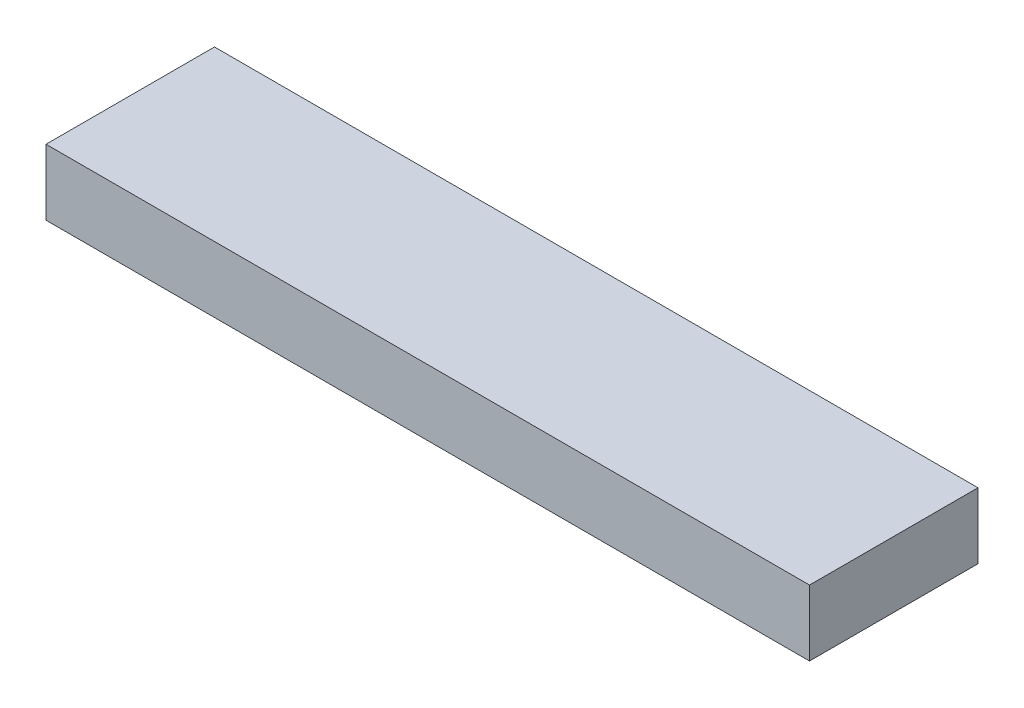
SolidWorks part; units mm, degrees
ref_plane "Front" through (0, 0, 0) normal (0, 0, 1) x (1, 0, 0)
ref_plane "Top" through (0, 0, 0) normal (0, 1, 0) x (1, 0, 0)
ref_plane "Right" through (0, 0, 0) normal (1, 0, 0) x (0, 0, -1)
sketch "Sketch1" plane through (0, 0, 0) normal (0, 1, 0) x (1, 0, 0)
  line L1 (-145, -32) -> (145, -32)
  line L2 (-145, -32) -> (-145, 32)
  line L3 (-145, 32) -> (145, 32)
  line L4 (145, -32) -> (145, 32)
  line L5 (-145, -32) -> (145, 32) construction
  line L6 (-145, 32) -> (145, -32) construction
  point P0 (0, 0)
  dimension "D1" = 290
  dimension "D2" = 64
extrude "Boss-Extrude1" add sketch "Sketch1" against normal blind 25
